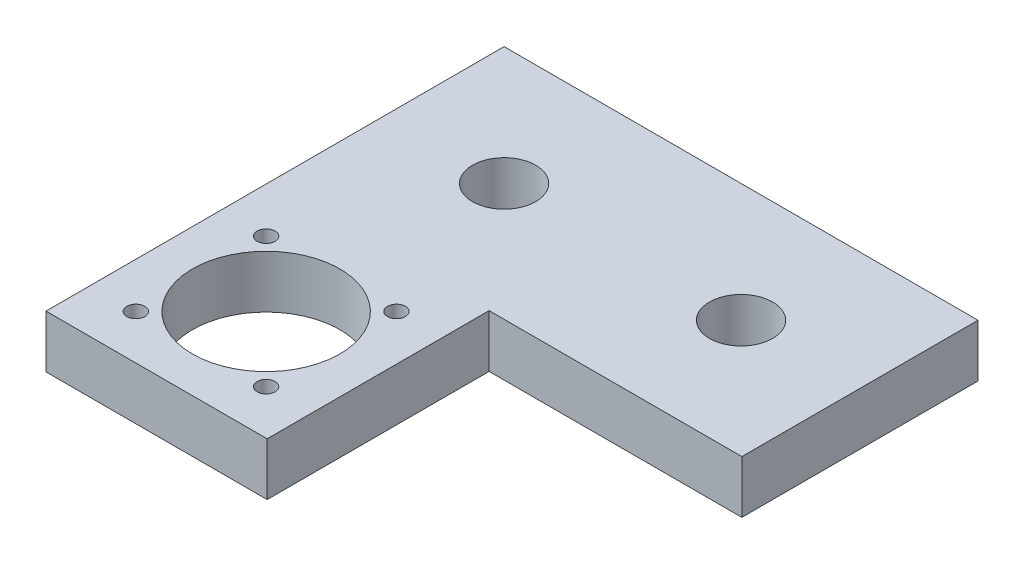
SolidWorks part; units mm, degrees
ref_plane "Спереди" through (0, 0, 0) normal (0, 0, 1) x (1, 0, 0)
ref_plane "Сверху" through (0, 0, 0) normal (0, 1, 0) x (1, 0, 0)
ref_plane "Справа" through (0, 0, 0) normal (1, 0, 0) x (0, 0, -1)
sketch "Эскиз1" plane through (0, 0, 0) normal (0, 1, 0) x (1, 0, 0)
  line L0 (42, 0.15) -> (89.9999, 0.15)
  line L2 (0, 0) -> (0, 45)
  line L3 (0, 45) -> (89.9999, 45)
  line L4 (89.9999, 0.15) -> (89.9999, 45)
  line L5 (0, -42) -> (42, -42)
  line L6 (0, 0) -> (0, -42)
  line L8 (42, 0.15) -> (42, -42)
  dimension "D1" = 45
  dimension "D2" = 90
  dimension "D3" = 42
extrude "Бобышка-Вытянуть1" add sketch "Эскиз1" along normal blind 10
sketch "Эскиз2" plane through (0, 10, 0) normal (0, 1, 0) x (1, 0, 0)
  line L0 (90, 57.9915) -> (45, 57.9915) construction
  line L1 (0, 57.9915) -> (45, 57.9915) construction
  circle A0 centre (67.5, 22.5) radius 6
  circle A1 centre (22.5, 22.5) radius 6
  dimension "D2" = 12
  dimension "D3" = 12
  dimension "D1" = 45
extrude "Вырез-Вытянуть1" cut sketch "Эскиз2" against normal through all
sketch "Эскиз3" plane through (0, 10, 0) normal (0, 1, 0) x (1, 0, 0)
  circle A0 centre (20.9594, -21.15) radius 14
  circle A1 centre (20.9594, -21.15) radius 17.5 construction
  circle A3 centre (33.3338, -33.5244) radius 1.7
  circle A5 centre (8.585, -33.5244) radius 1.7
  circle A7 centre (8.585, -8.7756) radius 1.7
  circle A9 centre (33.3338, -8.7756) radius 1.7
  point P22 (20.9594, -21.15)
  dimension "D1" = 28
  dimension "D2" = 35
extrude "Вырез-Вытянуть2" cut sketch "Эскиз3" against normal through all
